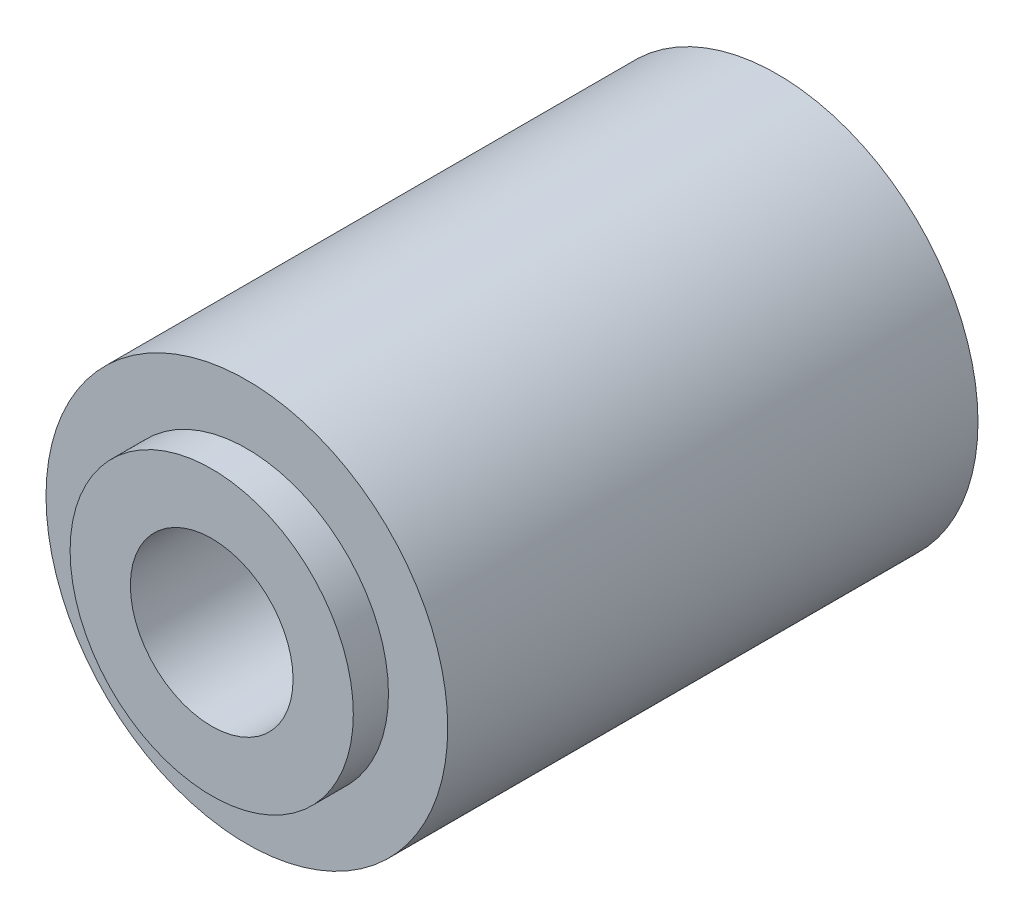
SolidWorks part; units mm, degrees
ref_plane "Alzado" through (0, 0, 0) normal (0, 0, 1) x (1, 0, 0)
ref_plane "Planta" through (0, 0, 0) normal (0, 1, 0) x (1, 0, 0)
ref_plane "Vista lateral" through (0, 0, 0) normal (1, 0, 0) x (0, 0, -1)
sketch "Croquis1" plane through (0, 0, 0) normal (0, 0, 1) x (1, 0, 0)
  circle A0 centre (0, 0) radius 10
  circle A1 centre (0, 0) radius 4.05
  dimension "D1" = 20
  dimension "D2" = 8.1
extrude "Saliente-Extruir1" add sketch "Croquis1" along normal blind 26.4
sketch "Croquis2" plane through (0, 0, 26.4) normal (0, 0, 1) x (1, 0, 0)
  circle A0 centre (0, 0) radius 7.05
  circle A1 centre (0, 0) radius 4.05
  circle A2 centre (0, 0) radius 4.05 construction
  dimension "D1" = 3
extrude "Saliente-Extruir2" add sketch "Croquis2" along normal blind 1.75
sketch "Croquis3" plane through (0, 0, 0) normal (0, 0, -1) x (-1, 0, 0)
  circle A0 centre (0, 0) radius 4.05
  circle A1 centre (0, 0) radius 4.05 construction
  circle A2 centre (0, 0) radius 7.05
  dimension "D1" = 3
extrude "Saliente-Extruir3" add sketch "Croquis3" along normal blind 1.75
